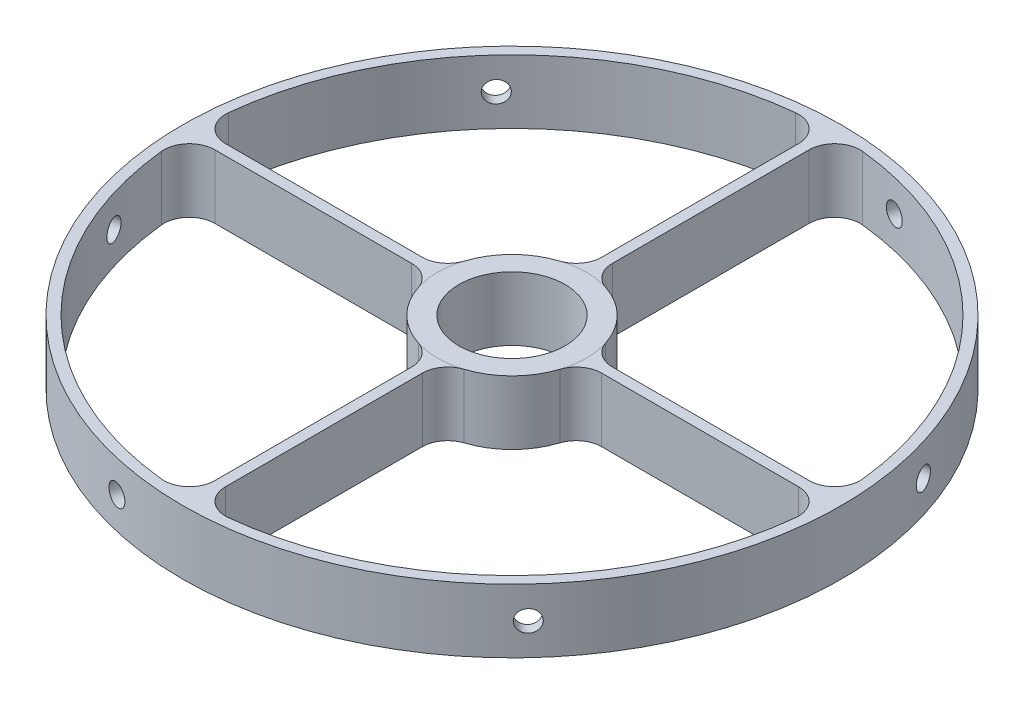
SolidWorks part; units mm, degrees
material "6061-T6 (SS)"
ref_plane "Front Plane" through (0, 0, 0) normal (0, 0, 1) x (1, 0, 0)
ref_plane "Top Plane" through (0, 0, 0) normal (0, 1, 0) x (1, 0, 0)
ref_plane "Right Plane" through (0, 0, 0) normal (1, 0, 0) x (0, 0, -1)
sketch "Center Ring" plane through (0, 0, 0) normal (0, 1, 0) x (1, 0, 0)
  circle A0 centre (0, 0) radius 15.875
  circle A1 centre (0, 0) radius 22.225
  dimension "D2" = 31.75
  dimension "D1" = 6.35
extrude "Center" add sketch "Center Ring" along normal mid plane 19.05
sketch "Outer " plane through (0, 0, 0) normal (0, 1, 0) x (1, 0, 0)
  circle A0 centre (0, 0) radius 98.425
  circle A1 centre (0, 0) radius 95.25
  dimension "D1" = 3.175
  dimension "D2" = 196.85
extrude "Outer Ring" add sketch "Outer " along normal mid plane 19.05 separate body
ref_plane "Plane1" through (0, 0, 47.625) normal (0, 0, 1) x (1, 0, 0)
sketch "beeam" plane through (0, 0, 47.625) normal (0, 0, 1) x (1, 0, 0)
  line L1 (-1.5875, -9.525) -> (1.5875, -9.525)
  line L2 (-1.5875, -9.525) -> (-1.5875, 9.525)
  line L3 (-1.5875, 9.525) -> (1.5875, 9.525)
  line L4 (1.5875, -9.525) -> (1.5875, 9.525)
  line L5 (-1.5875, -9.525) -> (1.5875, 9.525) construction
  line L6 (-1.5875, 9.525) -> (1.5875, -9.525) construction
  point P0 (0, 0)
  dimension "D1" = 3.175
  dimension "D2" = 19.05
extrude "Beam" add sketch "beeam" against normal up to surface and the other way up to surface
pattern_circular "CirPattern1" count 4 over 360 about axis through (0, 0, 0) along (0, 1, 0) of "Beam"
ref_plane "Plane2" through (0, 0, 100.0125) normal (0, 0, 1) x (1, 0, 0)
fillet "Fillet1" radius 7.62 16 edges at (1.5875, 0, -22.1682) (22.1682, 0, -1.5875) (22.1682, 0, 1.5875) (1.5875, 0, 22.1682) (-22.1682, 0, 1.5875) (-1.5875, 0, 22.1682) (-22.1682, 0, -1.5875) (-1.5875, 0, -22.1682) (1.5875, 0, 95.2368) (-1.5875, 0, 95.2368) (-95.2368, 0, 1.5875) (-95.2368, 0, -1.5875) (95.2368, 0, 1.5875) (95.2368, 0, -1.5875) (1.5875, 0, -95.2368) (-1.5875, 0, -95.2368)
sketch "Sketch9" plane through (0, 9.525, 0) normal (0, 1, 0) x (1, 0, 0)
  circle A0 centre (0, 0) radius 15.875
  dimension "D1" = 31.75
sketch "Sketch10" plane through (0, 9.525, 0) normal (0, 1, 0) x (1, 0, 0)
  circle A0 centre (0, 0) radius 22.225
  dimension "D1" = 44.45
split line "Split Line2"
ref_plane "Plane4" through (71.9835, 0, 67.1257) normal (0.7314, 0, 0.682) x (0, -1, 0)
sketch "Sketch13" plane through (71.9835, 0, 67.1257) normal (0.7314, 0, 0.682) x (0, -1, 0)
  circle A0 centre (0, 0) radius 3.175
  dimension "D1" = 6.35
extrude "Cut-Extrude2" cut sketch "Sketch13" against normal up to next
pattern_circular "CirPattern3" count 6 over 360 about axis through (0, 9.525, 0) along (0, -1, 0) of "Cut-Extrude2"
equation "\"a\"= .125'Width of the Beams"
equation "\"D1@beeam\" = \"a\""
equation "\"T\"= .125'Width of the Outer Ring"
equation "\"D1@Outer \" = \"T\""
equation "\"R\"= .25'Thickness of the Center"
equation "\"D1@Center Ring\" = \"R\""
equation "\"H\"= .75'Height (Outer Ring/Center)"
equation "\"D1@Outer Ring\"= \"H\""
equation "\"D1@Center\"=\"H\""
equation "\"I\"= .75'Height (Beams)"
equation "\"N\"= 4'Number of Beams"
equation "\"D1@CirPattern1\"=\"N\""
equation "\"D2@beeam\"=\"I\""
equation "\"D\"= 1.5'Diameter of the Center"
